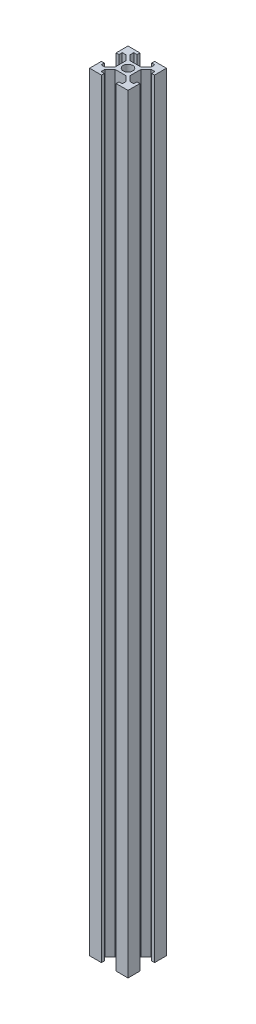
SolidWorks part; units mm, degrees
ref_plane "前视基准面" through (0, 0, 0) normal (0, 0, 1) x (1, 0, 0)
ref_plane "上视基准面" through (0, 0, 0) normal (0, 1, 0) x (1, 0, 0)
ref_plane "右视基准面" through (0, 0, 0) normal (1, 0, 0) x (0, 0, -1)
sketch "草图1" plane through (0, 0, 0) normal (0, 1, 0) x (1, 0, 0)
  line L0 (-6.5607, 5.5) -> (-3.9, 2.8393)
  line L1 (-10, 10) -> (10, 10)
  line L2 (-10, 10) -> (-10, -10)
  line L3 (-10, -10) -> (10, -10)
  line L4 (10, 10) -> (10, -10)
  line L5 (-10, 10) -> (10, -10) construction
  line L6 (-10, -10) -> (10, 10) construction
  line L7 (-3.9, 3.9) -> (3.9, 3.9)
  line L8 (-3.9, 3.9) -> (-3.9, -3.9)
  line L9 (-3.9, -3.9) -> (3.9, -3.9)
  line L10 (3.9, 3.9) -> (3.9, -3.9)
  line L11 (-3.9, 3.9) -> (3.9, -3.9) construction
  line L12 (-3.9, -3.9) -> (3.9, 3.9) construction
  line L13 (-10, 10) -> (-5.5, 10)
  line L14 (-10, 10) -> (-10, 5.5)
  line L15 (-10, 5.5) -> (-5.5, 5.5)
  line L16 (-5.5, 10) -> (-5.5, 5.5)
  line L17 (-10, 5.5) -> (-8.5, 5.5)
  line L18 (-10, 5.5) -> (-10, 3.8)
  line L19 (-10, 3.8) -> (-8.5, 3.8)
  line L20 (-8.5, 5.5) -> (-8.5, 3.8)
  line L21 (-5.5, 6.5607) -> (-2.8393, 3.9)
  line L22 (-3.8, 10) -> (-3.8, 8.5)
  line L23 (-5.5, 8.5) -> (-3.8, 8.5)
  line L24 (0, 10) -> (0, -10) construction
  line L25 (5.5, 8.5) -> (3.8, 8.5)
  line L26 (3.8, 10) -> (3.8, 8.5)
  line L27 (5.5, 6.5607) -> (2.8393, 3.9)
  line L28 (6.5607, 5.5) -> (3.9, 2.8393)
  line L29 (10, 3.8) -> (8.5, 3.8)
  line L30 (8.5, 5.5) -> (8.5, 3.8)
  line L31 (10, 5.5) -> (8.5, 5.5)
  line L32 (10, 5.5) -> (10, 3.8)
  line L33 (10, 5.5) -> (5.5, 5.5)
  line L34 (5.5, 10) -> (5.5, 5.5)
  line L35 (10, 10) -> (5.5, 10)
  line L36 (10, 10) -> (10, 5.5)
  line L37 (-10, 0) -> (10, 0) construction
  line L38 (-10, -3.8) -> (-8.5, -3.8)
  line L39 (-8.5, -5.5) -> (-8.5, -3.8)
  line L40 (-10, -5.5) -> (-5.5, -5.5)
  line L41 (-6.5607, -5.5) -> (-3.9, -2.8393)
  line L42 (-5.5, -6.5607) -> (-2.8393, -3.9)
  line L43 (-5.5, -10) -> (-5.5, -5.5)
  line L44 (-5.5, -8.5) -> (-3.8, -8.5)
  line L45 (-3.8, -10) -> (-3.8, -8.5)
  line L46 (3.8, -10) -> (3.8, -8.5)
  line L47 (6.5607, -5.5) -> (3.9, -2.8393)
  line L48 (5.5, -6.5607) -> (2.8393, -3.9)
  line L49 (-10, 10) -> (10, 10)
  line L50 (-10, -10) -> (10, -10)
  line L51 (5.5, -8.5) -> (3.8, -8.5)
  line L52 (5.5, -10) -> (5.5, -5.5)
  line L53 (10, -5.5) -> (5.5, -5.5)
  line L54 (10, -3.8) -> (8.5, -3.8)
  line L55 (8.5, -5.5) -> (8.5, -3.8)
  circle A0 centre (0, 0) radius 2.5
  dimension "D1" = 5
  dimension "D2" = 20
  dimension "D3" = 20
  dimension "D4" = 7.8
  dimension "D5" = 4.5
  dimension "D6" = 1.7
  dimension "D7" = 0.75
  dimension "D8" = 1.5
extrude "凸台-拉伸1" add sketch "草图1" along normal blind 400 contours L1 L34 L33 L31 L4 | L4 L31 L30 L29 | L34 L27 L7 L10 L28 L33 | L34 L1 L26 L25 | L10 L7 L8 L9 A0 | L16 L23 L22 L1 | L16 L1 L2 L15 | L20 L15 L2 L19 | L21 L16 L15 L0 L8 L7 | L3 L43 L40 L2 | L3 L45 L44 L43 | L2 L40 L39 L38 | L43 L42 L9 L8 L41 L40 | L53 L47 L10 L9 L48 L52 | L4 L53 L52 L50 | L55 L53 L4 L54 | L3 L52 L51 L46
